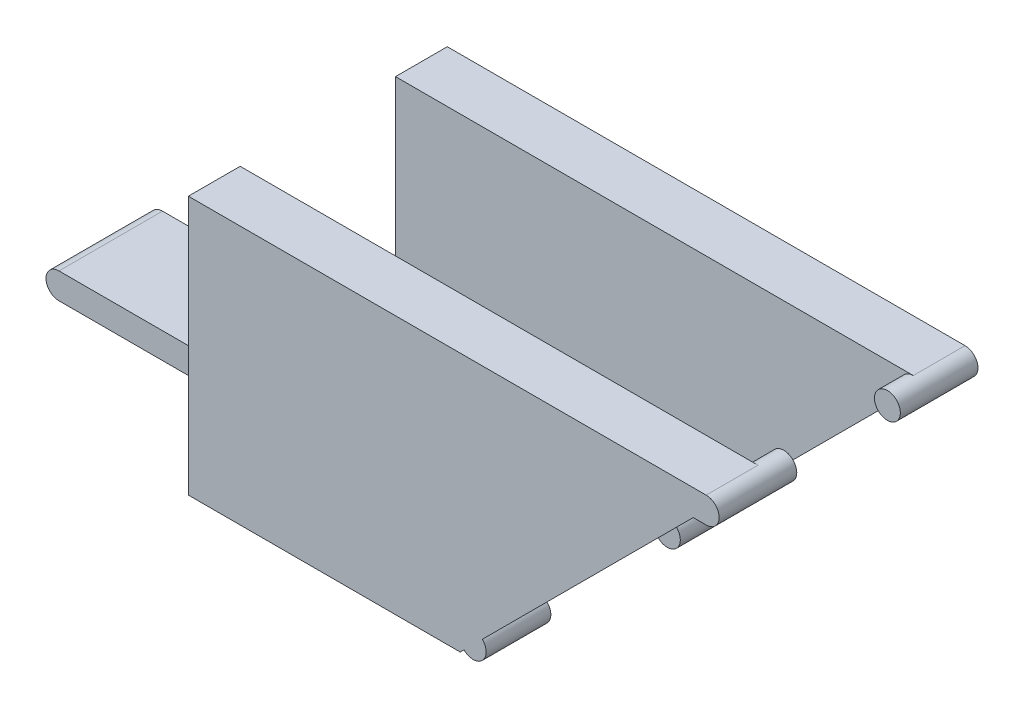
SolidWorks part; units mm, degrees
ref_plane "Front" through (0, 0, 0) normal (0, 0, 1) x (1, 0, 0)
ref_plane "Top" through (0, 0, 0) normal (0, 1, 0) x (1, 0, 0)
ref_plane "Right" through (0, 0, 0) normal (1, 0, 0) x (0, 0, -1)
sketch "草图1" plane through (0, 0, 0) normal (0, 1, 0) x (1, 0, 0)
  line L1 (-2, 10) -> (38, 10)
  line L2 (-2, 10) -> (-2, -10)
  line L3 (-2, -10) -> (38, -10)
  line L4 (38, 10) -> (38, -10)
  dimension "D1" = 40
  dimension "D2" = 38
  dimension "D3" = 20
  dimension "D4" = 10
extrude "凸台-拉伸1" add sketch "草图1" along normal blind 20
sketch "草图2" plane through (-2, 0, 0) normal (-1, 0, 0) x (0, 0, 1)
  line L0 (-10, 0) -> (10, 0) construction
  line L1 (-4, 0) -> (4, 0)
  line L2 (-4, 0) -> (-4, 4)
  line L3 (-4, 4) -> (4, 4)
  line L4 (4, 0) -> (4, 4)
  line L5 (0, 0) -> (0, 20) construction
  line L6 (-10, 20) -> (10, 20) construction
  dimension "D1" = 4
  dimension "D2" = 8
  dimension "D3" = 4
extrude "凸台-拉伸2" add sketch "草图2" along normal blind 16
sketch "草图4" plane through (-2, 0, 0) normal (-1, 0, 0) x (0, 0, 1)
  line L0 (-3.6152, 4) -> (13.732, 4) construction
  line L2 (-6, 22.3249) -> (6, 22.3249)
  line L3 (-6, 22.3249) -> (-6, 4)
  line L4 (-6, 4) -> (6, 4)
  line L5 (6, 22.3249) -> (6, 4)
  dimension "D1" = 12
  dimension "D2" = 6
extrude "切除-拉伸2" cut sketch "草图4" against normal through all
sketch "草图7" plane through (38, 0, 0) normal (1, 0, 0) x (0, 0, -1)
  line L0 (-10, 0) -> (10, 0) construction
  line L1 (-6, 4) -> (6, 4)
  line L2 (-6, 4) -> (-6, 0)
  line L3 (-6, 0) -> (6, 0)
  line L4 (6, 4) -> (6, 0)
extrude "切除-拉伸4" cut sketch "草图7" against normal blind 20
sketch "草图5" plane through (0, 0, 0) normal (0, 0, 1) x (1, 0, 0)
  line L0 (38, 20) -> (38, 0) construction
  line L1 (0, 0) -> (38, 0) construction
  circle A0 centre (38, 19) radius 1
  circle A1 centre (38, 1) radius 1
extrude "凸台-拉伸3" add sketch "草图5" along normal mid plane 20
sketch "草图6" plane through (38, 0, 0) normal (1, 0, 0) x (0, 0, -1)
  line L0 (0, 0) -> (0, 25.6399) construction
  line L2 (-4, 22.9943) -> (4, 22.9943)
  line L3 (-4, 22.9943) -> (-4, -2.0443)
  line L4 (-4, -2.0443) -> (4, -2.0443)
  line L5 (4, 22.9943) -> (4, -2.0443)
  dimension "D1" = 8
  dimension "D2" = 4
extrude "切除-拉伸3" cut sketch "草图6" against normal mid plane 20
sketch "草图12" plane through (0, 0, 4) normal (0, 0, 1) x (1, 0, 0)
  line L1 (-5, 2) -> (-18.4748, 2)
  line L3 (-5, 0) -> (-18.4748, 0)
  line L4 (-18.4748, 2) -> (-18.4748, 0)
  arc A0 (-5, 2) -> (-5, 0) centre (-5, 1) ccw
extrude "切除-拉伸8" cut sketch "草图12" against normal blind 20
sketch "草图13" plane through (0, 0, 4) normal (0, 0, 1) x (1, 0, 0)
  line L0 (-18, 2) -> (-18, 4) construction
  circle A0 centre (-18, 3) radius 1
extrude "凸台-拉伸5" add sketch "草图13" against normal blind 8
sketch "草图15" plane through (0, 0, 10) normal (0, 0, 1) x (1, 0, 0)
  line L0 (38, 19) -> (15.8051, -3.1949) construction
  line L1 (19, 0) -> (39.888, 0)
  line L2 (-2, 0) -> (38, 0) construction
  line L3 (39.888, 0) -> (38, 18)
  line L4 (38, 18) -> (37, 18)
  line L5 (37, 18) -> (19, 0)
extrude "切除-拉伸10" cut sketch "草图15" against normal blind 20
sketch "草图16" plane through (0, 0, 10) normal (0, 0, 1) x (1, 0, 0)
  line L0 (-5, 1) -> (21.2991, 1) construction
  circle A0 centre (20, 1) radius 1
extrude "凸台-拉伸12" add sketch "草图16" against normal blind 5
sketch "草图17" plane through (0, 0, -10) normal (0, 0, -1) x (-1, 0, 0)
  circle A0 centre (-20, 1) radius 1
extrude "凸台-拉伸13" add sketch "草图17" against normal blind 5
